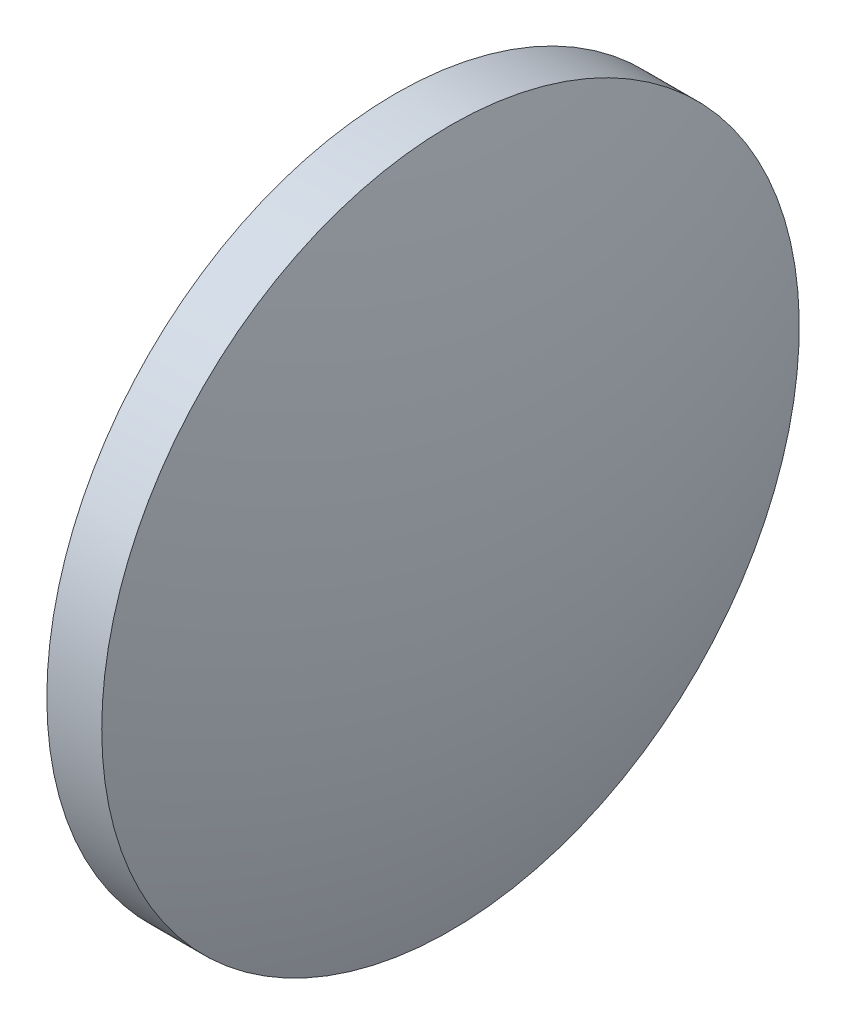
SolidWorks part; units mm, degrees
ref_plane "前视基准面" through (0, 0, 0) normal (0, 0, 1) x (1, 0, 0)
ref_plane "上视基准面" through (0, 0, 0) normal (0, 1, 0) x (1, 0, 0)
ref_plane "右视基准面" through (0, 0, 0) normal (1, 0, 0) x (0, 0, -1)
sketch "草图1" plane through (0, 0, 0) normal (0, 0, 1) x (1, 0, 0)
  line L0 (79.3054, 48.6161) -> (93.4772, 48.6161) construction
  line L1 (85.4585, 61.3161) -> (87.4579, 61.3161)
  line L2 (87.4579, 61.3161) -> (87.4579, 35.9161)
  line L3 (87.4579, 35.9161) -> (85.4585, 35.9161)
  line L4 (85.4585, 35.9161) -> (85.4585, 61.3161)
  arc A0 (85.4585, 61.3161) -> (85.4585, 35.9161) centre (125.833, 48.6161) ccw
  arc A1 (87.4579, 35.9161) -> (87.4579, 61.3161) centre (47.0834, 48.6161) ccw
  dimension "D1" = 25.4
  dimension "D2" = 1.9993
revolve "旋转1" add sketch "草图1" angle 360 about L0
